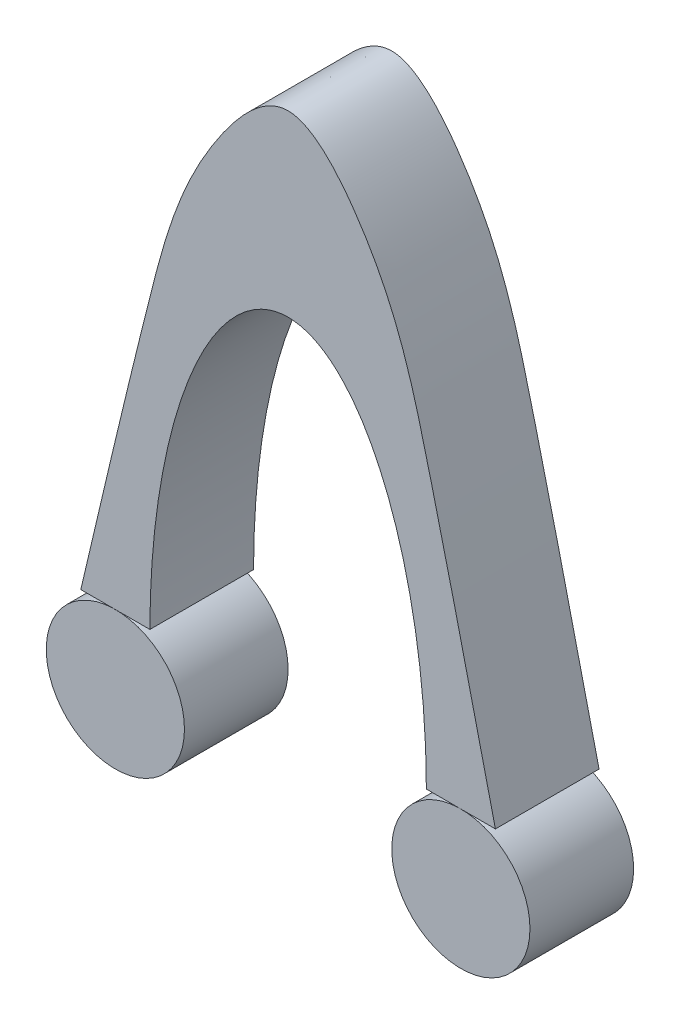
SolidWorks part; units mm, degrees
ref_plane "Front" through (0, 0, 0) normal (0, 0, 1) x (1, 0, 0)
ref_plane "Top" through (0, 0, 0) normal (0, 1, 0) x (1, 0, 0)
ref_plane "Right" through (0, 0, 0) normal (1, 0, 0) x (0, 0, -1)
sketch "Sketch1" plane through (0, 0, 0) normal (0, 0, 1) x (1, 0, 0)
  line L0 (-60, 0) -> (-40, 0)
  line L1 (40, 0) -> (60, 0)
  ellipse E0 centre (0, 0) end of major axis (0, 98.2708) minor radius 40 (40, 0) -> (-40, 0) ccw
  spline S0 degree 3 poles (-60, 0) (-53.3733, 28.3024) (-42.5826, 74.3895) (-29.4013, 124.1221) (0, 158.4334) (29.4013, 124.1221) (42.5826, 74.3895) (53.3733, 28.3024) (60, 0) knots 0 0 0 0 0.258778 0.421388 0.5 0.578612 0.741222 1 1 1 1
  point P27 (0, 50)
  point P29 (0, 100)
extrude "Extrude1" add sketch "Sketch1" along normal mid plane 30
sketch "Sketch2" plane through (0, 0, 0) normal (0, 0, 1) x (1, 0, 0)
  circle A0 centre (50, -20) radius 20
  circle A1 centre (-50, -20) radius 20
extrude "Extrude2" add sketch "Sketch2" along normal mid plane 30
